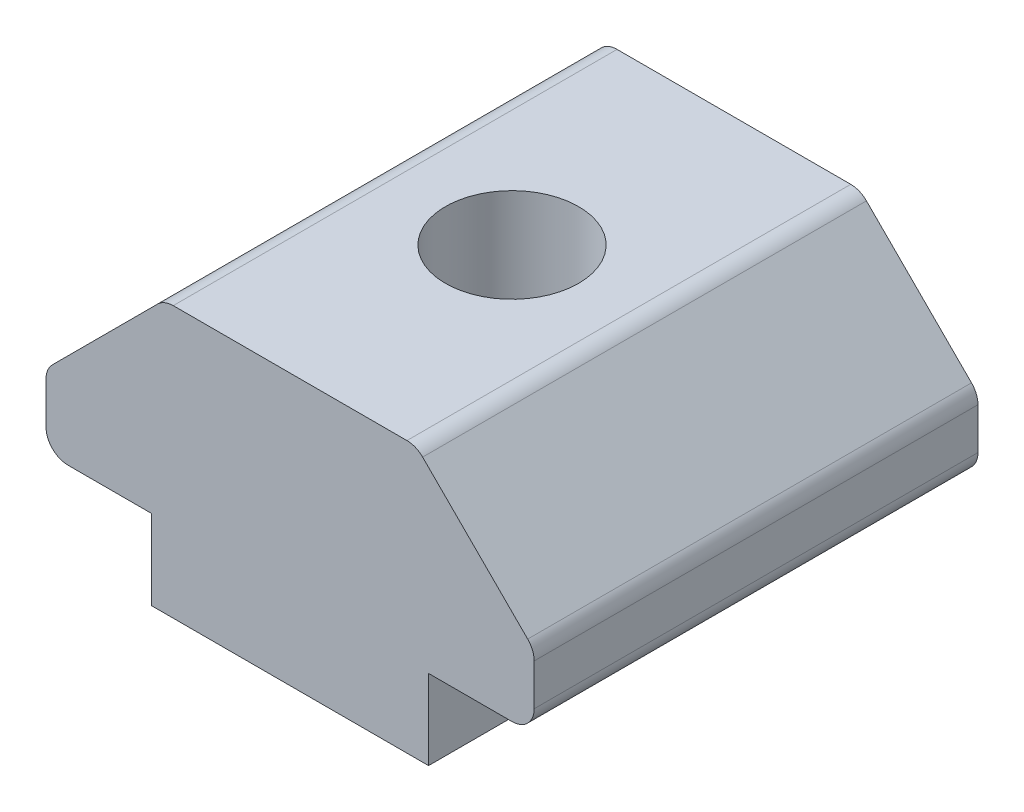
SolidWorks part; units mm, degrees
ref_plane "Alzado" through (0, 0, 0) normal (0, 0, 1) x (1, 0, 0)
ref_plane "Planta" through (0, 0, 0) normal (0, 1, 0) x (1, 0, 0)
ref_plane "Vista lateral" through (0, 0, 0) normal (1, 0, 0) x (0, 0, -1)
sketch "Croquis1" plane through (0, 0, 0) normal (0, 0, 1) x (-1, 0, 0)
  line L0 (4.5, -1.7993) -> (4.5, -3.4393)
  line L1 (4.5, -3.4393) -> (7.16, -6.0993)
  line L4 (7.16, -6.0993) -> (9.75, -6.0993)
  line L5 (9.75, -6.0993) -> (12.84, -6.0993)
  line L7 (12.84, -6.0993) -> (15.5, -3.4393)
  line L8 (15.5, -3.4393) -> (15.5, -1.7993)
  line L9 (15.5, -1.7993) -> (4.5, -1.7993)
extrude "Saliente-Extruir1" add sketch "Croquis1" along normal blind 10
fillet "Redondeo1" radius 0.5 1 edges at (-15.5, 1.7993, 5)
fillet "Redondeo2" radius 0.5 5 edges at (-15.5, 3.4393, 5) (-12.84, 6.0993, 5) (-7.16, 6.0993, 5) (-4.5, 3.4393, 5) (-4.5, 1.7993, 5)
sketch "Croquis3" plane through (0, 0, 10) normal (0, 0, 1) x (1, 0, 0)
  line L0 (-15.5, 2.2993) -> (-13.12, 2.2993) construction
  line L1 (-4.5, 2.2993) -> (-6.88, 2.2993) construction
  line L2 (-13.12, 1.7993) -> (-13.12, -0.0007)
  line L3 (-15, 1.7993) -> (-5, 1.7993) construction
  line L4 (-13.12, -0.0007) -> (-6.88, -0.0007)
  line L5 (-6.88, -0.0007) -> (-6.88, 1.7993)
  line L6 (-6.88, 1.7993) -> (-13.12, 1.7993)
  dimension "D1" = 2.38
  dimension "D2" = 2.38
  dimension "D3" = 1.8
extrude "Saliente-Extruir2" add sketch "Croquis3" against normal blind 10 contours L5 L6 L2 L4
sketch "Croquis2" plane through (0, 1.7993, 0) normal (0, -1, 0) x (-1, 0, 0)
  line L0 (10, -10) -> (10, 0) construction
  line L1 (15.5, -10) -> (4.5, -10) construction
  line L2 (15.5, 0) -> (4.5, 0) construction
  circle A0 centre (10, -5) radius 1.5
extrude "Cortar-Extruir1" cut sketch "Croquis2" against normal through all both and the other way through all contours A0
